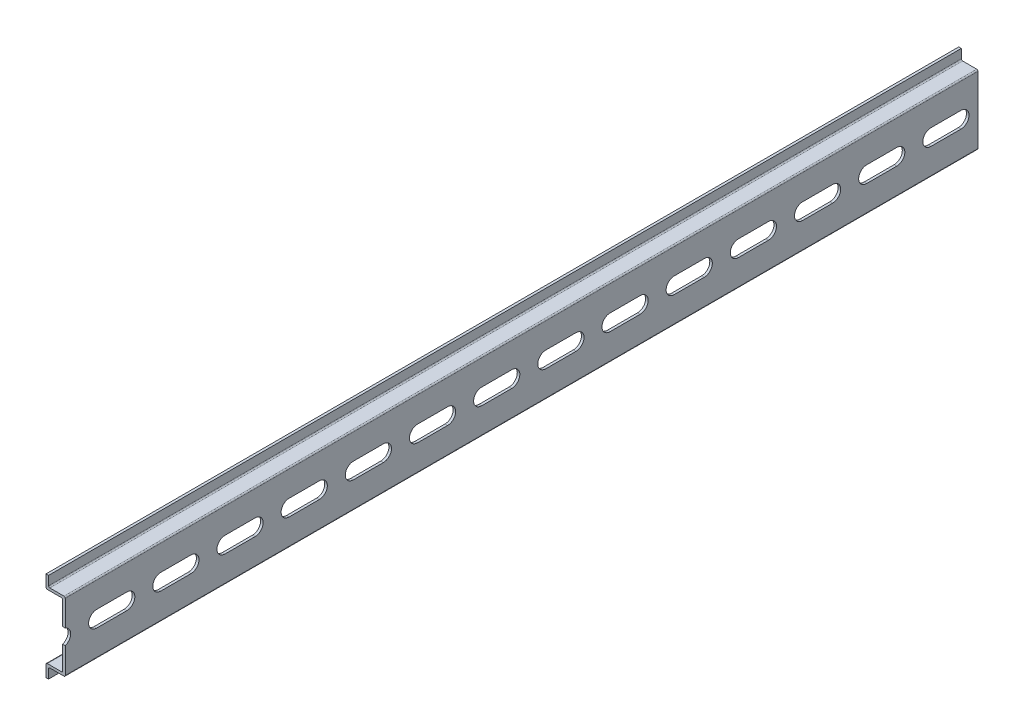
SolidWorks part; units mm, degrees
ref_plane "Front Plane" through (0, 0, 0) normal (0, 0, 1) x (1, 0, 0)
ref_plane "Top Plane" through (0, 0, 0) normal (0, 1, 0) x (1, 0, 0)
ref_plane "Right Plane" through (0, 0, 0) normal (1, 0, 0) x (0, 0, -1)
sketch "profile" plane through (0, 0, 0) normal (0, 0, 1) x (1, 0, 0)
  line L0 (0, -13.5) -> (0, 13.5) construction
  line L1 (0, 13.5) -> (-6.5, 13.5) construction
  line L2 (-6.5, 13.5) -> (-6.5, 17.5) construction
  line L3 (0, -13.5) -> (-6.5, -13.5) construction
  line L4 (-6.5, -13.5) -> (-6.5, -17.5) construction
  dimension "D1" = 27
  dimension "D2" = 35
  dimension "D3" = 6.5
sketch "Sketch3" plane through (0, 0, 0) normal (0, 0, 1) x (1, 0, 0)
  line L0 (-6.5, -13.5) -> (-6.5, -17.5) construction
  line L1 (0, -13.5) -> (-6.5, -13.5) construction
  line L2 (0, -13.5) -> (0, 13.5) construction
  line L3 (0, 13.5) -> (-6.5, 13.5) construction
  line L4 (-6.5, 13.5) -> (-6.5, 17.5) construction
  line L5 (-6.5, -13.5) -> (-6.5, -17.5)
  line L6 (0, -13.5) -> (-6.5, -13.5)
  line L7 (0, -13.5) -> (0, 13.5)
  line L8 (0, 13.5) -> (-6.5, 13.5)
  line L9 (-6.5, 13.5) -> (-6.5, 17.5)
extrude "Extrude-Thin1" add sketch "Sketch3" along normal blind 449.2625 thin
sketch "Sketch4" plane through (0, 0, 0) normal (1, 0, 0) x (0, 0, -1)
  line L0 (0, 0) -> (-62.1077, 0) construction
  line L1 (-6.65, 0) -> (-18.35, 0) construction
  line L2 (-6.65, -3.15) -> (-18.35, -3.15)
  line L3 (-6.65, 3.15) -> (-18.35, 3.15)
  arc A0 (-6.65, -3.15) -> (-6.65, 3.15) centre (-6.65, 0) ccw
  arc A1 (-18.35, 3.15) -> (-18.35, -3.15) centre (-18.35, 0) ccw
  point P5 (-12.5, 0)
  point P10 (-3.5, 0)
  point P11 (-21.5, 0)
  point P12 (-37.5, 0)
  dimension "D1" = 18
  dimension "D2" = 6.3
  dimension "D3" = 12.5
  dimension "D4" = 25
extrude "Cut-Extrude1" cut sketch "Sketch4" against normal through all both and the other way through all
pattern_linear "LPattern1" count 18 spacing 25 along (0, 0, 1) of "Cut-Extrude1"
fillet "Fillet1" radius 0.5 8 edges at (0, -13.5, 224.6312) (0, 13.5, 224.6312) (-6.5, 13.5, 224.6312) (-6.5, -13.5, 224.6312) (-1, 12.5, 224.6312) (-1, -12.5, 224.6312) (-7.5, -12.5, 224.6312) (-7.5, 12.5, 224.6312)
ref_plane "Contact Plane 1" through (-1, 0, 0) normal (-1, 0, 0) x (0, 0, 1)
sketch "Sketch5" plane through (0, 0, 449.2625) normal (0, 0, 1) x (1, 0, 0)
  line L1 (-10.3164, 18.8536) -> (4.2273, 18.8536)
  line L2 (-10.3164, 18.8536) -> (-10.3164, -19.4946)
  line L3 (-10.3164, -19.4946) -> (4.2273, -19.4946)
  line L4 (4.2273, 18.8536) -> (4.2273, -19.4946)
extrude "Cut-Extrude2" cut sketch "Sketch5" against normal blind 93.6625
equation "\"D3@LPattern1\"=\"D4@Sketch4\""
equation "\"D1@LPattern1\" = \"Length@Extrude-Thin1\" / \"D3@LPattern1\""
